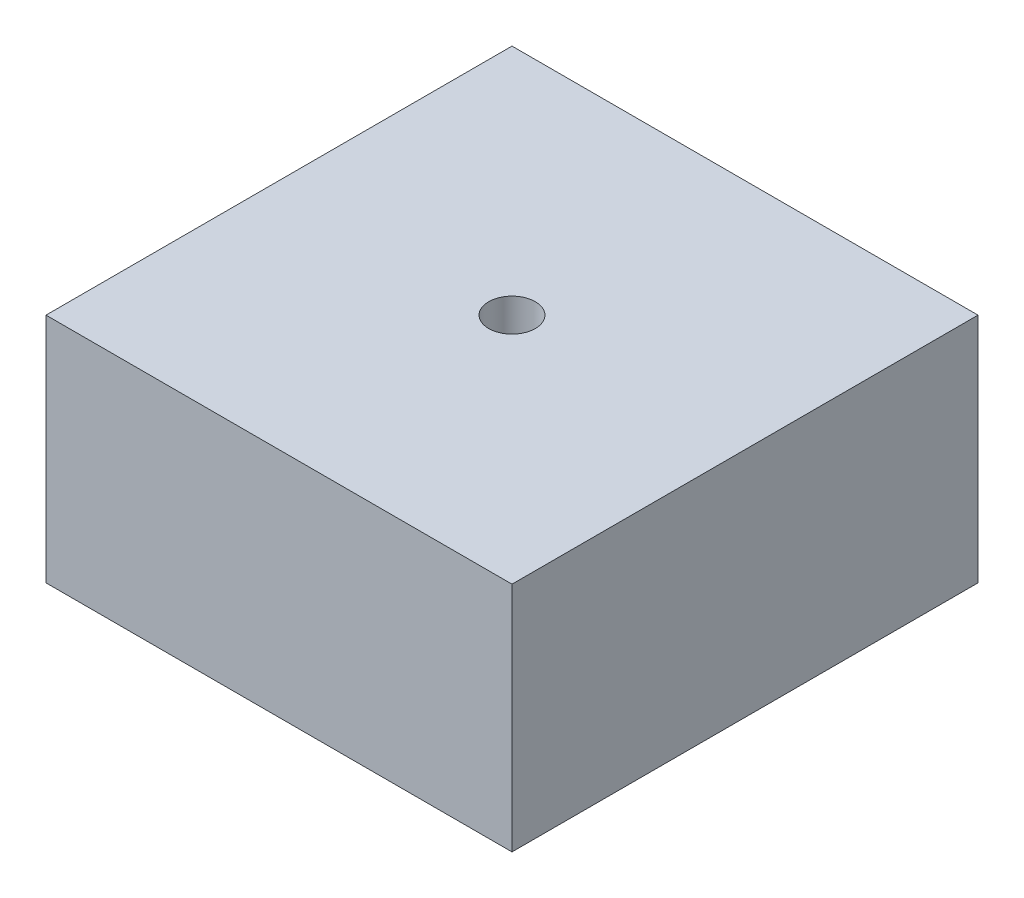
SolidWorks part; units mm, degrees
ref_plane "Front Plane" through (0, 0, 0) normal (0, 0, 1) x (1, 0, 0)
ref_plane "Top Plane" through (0, 0, 0) normal (0, 1, 0) x (1, 0, 0)
ref_plane "Right Plane" through (0, 0, 0) normal (1, 0, 0) x (0, 0, -1)
ref_plane "Plane1" through (0, 0, 0) normal (0, 1, 0) x (-1, 0, 0)
sketch "Sketch1" plane through (0, 0, 0) normal (0, 1, 0) x (1, 0, 0)
  line L1 (-50, -50) -> (50, -50)
  line L2 (-50, -50) -> (-50, 50)
  line L3 (-50, 50) -> (50, 50)
  line L4 (50, -50) -> (50, 50)
  line L5 (-50, -50) -> (50, 50) construction
  line L6 (-50, 50) -> (50, -50) construction
  point P0 (0, 0)
  dimension "D1" = 100
extrude "Boss-Extrude1" add sketch "Sketch1" along normal blind 49.7625
sketch "Sketch2" plane through (0, 49.7625, 0) normal (0, 1, 0) x (-1, 0, 0)
  circle A0 centre (0, 0) radius 5
  dimension "D1" = 10
extrude "Cut-Extrude1" cut sketch "Sketch2" against normal through all
